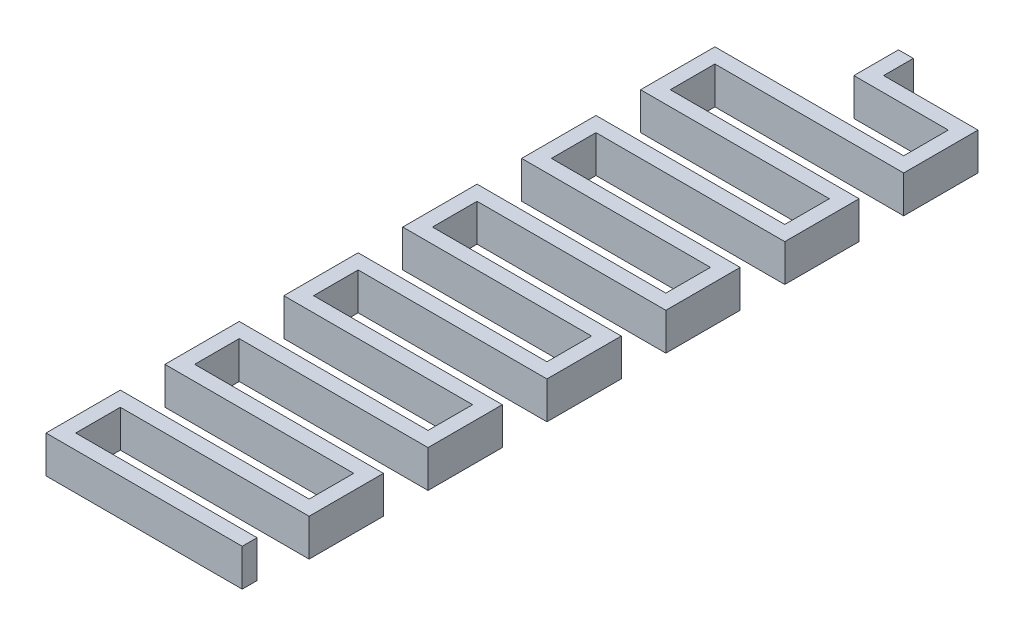
SolidWorks part; units mm, degrees
ref_plane "Front Plane" through (0, 0, 0) normal (0, 0, 1) x (1, 0, 0)
ref_plane "Top Plane" through (0, 0, 0) normal (0, 1, 0) x (1, 0, 0)
ref_plane "Right Plane" through (0, 0, 0) normal (1, 0, 0) x (0, 0, -1)
sketch "Sketch1" plane through (0, 0, 0) normal (0, 1, 0) x (1, 0, 0)
  line L0 (0, 0) -> (0, -5)
  line L5 (0, -5) -> (12.7, -5)
  line L6 (12.7, -5) -> (12.7, -13)
  line L7 (12.7, -13) -> (-12.7, -13)
  line L8 (-12.7, -13) -> (-12.7, -21)
  line L9 (-12.7, -21) -> (12.7, -21)
  line L10 (-12.7, -37) -> (12.7, -37)
  line L11 (-12.7, -29) -> (-12.7, -37)
  line L12 (12.7, -29) -> (-12.7, -29)
  line L13 (12.7, -21) -> (12.7, -29)
  line L14 (-12.7, -53) -> (12.7, -53)
  line L15 (-12.7, -45) -> (-12.7, -53)
  line L16 (12.7, -45) -> (-12.7, -45)
  line L17 (12.7, -37) -> (12.7, -45)
  line L18 (-12.7, -69) -> (12.7, -69)
  line L19 (-12.7, -61) -> (-12.7, -69)
  line L20 (12.7, -61) -> (-12.7, -61)
  line L21 (12.7, -53) -> (12.7, -61)
  line L22 (-12.7, -85) -> (12.7, -85)
  line L23 (-12.7, -77) -> (-12.7, -85)
  line L24 (12.7, -77) -> (-12.7, -77)
  line L25 (12.7, -69) -> (12.7, -77)
  line L26 (-12.7, -101) -> (12.7, -101)
  line L27 (-12.7, -93) -> (-12.7, -101)
  line L28 (12.7, -93) -> (-12.7, -93)
  line L29 (12.7, -85) -> (12.7, -93)
  dimension "D1" = 5
  dimension "D2" = 12.7
  dimension "D3" = 8
  dimension "D4" = 25.4
  dimension "D5" = 6
extrude "Extrude-Thin1" add sketch "Sketch1" along normal blind 5 thin thin type mid plane wall 2
